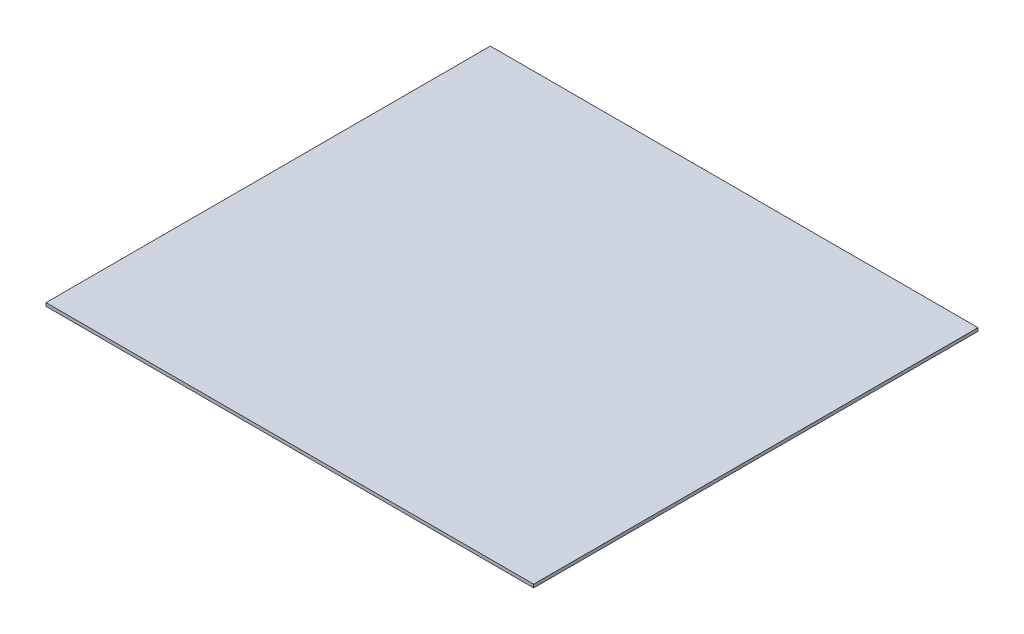
SolidWorks part; units mm, degrees
material "Acrylic (Medium-high impact)"
ref_plane "Front Plane" through (0, 0, 0) normal (0, 0, 1) x (1, 0, 0)
ref_plane "Top Plane" through (0, 0, 0) normal (0, 1, 0) x (1, 0, 0)
ref_plane "Right Plane" through (0, 0, 0) normal (1, 0, 0) x (0, 0, -1)
sketch "Sketch1" plane through (0, 0, 0) normal (0, 1, 0) x (1, 0, 0)
  line L1 (-225, -205) -> (225, -205)
  line L2 (-225, -205) -> (-225, 205)
  line L3 (-225, 205) -> (225, 205)
  line L4 (225, -205) -> (225, 205)
  line L5 (-225, -205) -> (225, 205) construction
  line L6 (-225, 205) -> (225, -205) construction
  point P0 (0, 0)
  dimension "D1" = 450
  dimension "D2" = 410
extrude "Boss-Extrude1" add sketch "Sketch1" along normal mid plane 3
